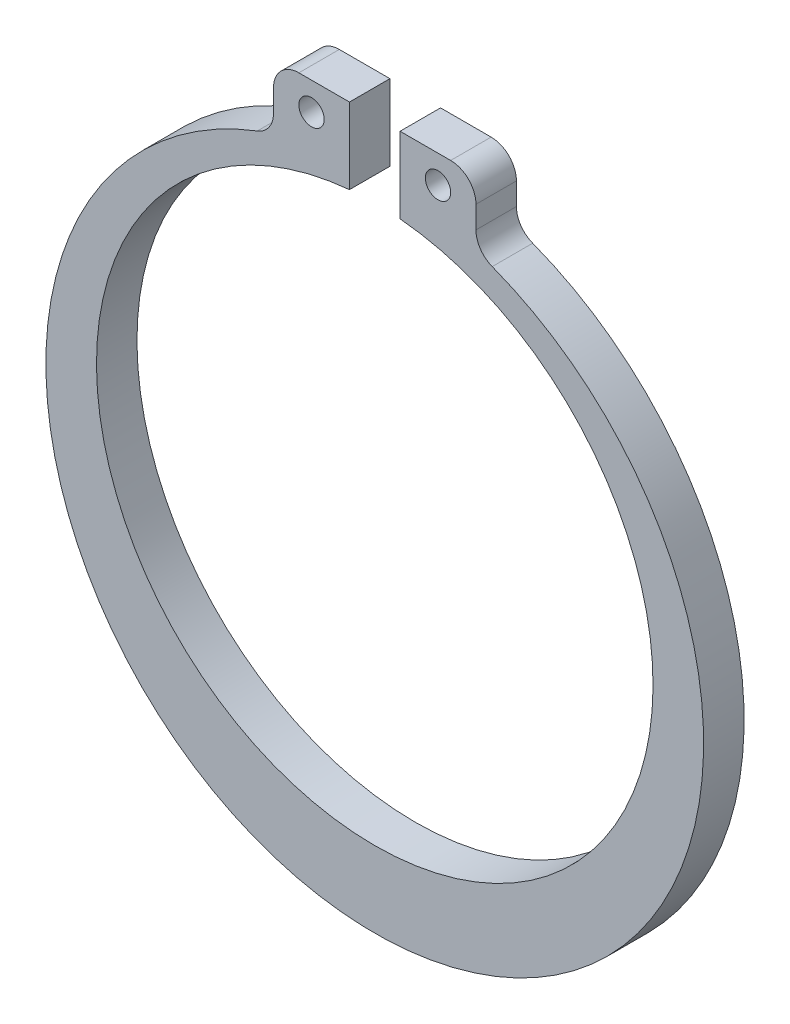
SolidWorks part; units mm, degrees
material "Сталь"
ref_plane "Спереди" through (0, 0, 0) normal (0, 0, 1) x (1, 0, 0)
ref_plane "Сверху" through (0, 0, 0) normal (0, 1, 0) x (1, 0, 0)
ref_plane "Справа" through (0, 0, 0) normal (1, 0, 0) x (0, 0, -1)
sketch "Эскиз1" plane through (0, 0, 0) normal (0, 0, 1) x (1, 0, 0)
  line L0 (0, -9.3116) -> (0, 9.3116) construction
  line L1 (0.5, 6.9772) -> (0.5, 5.4772)
  line L2 (0, -5.5) -> (0, -7)
  line L3 (0.5, 6.9772) -> (2, 6.9772)
  line L4 (2, 6.9772) -> (2, 5.6847)
  line L5 (1.25, 6.9772) -> (1.25, 5.8787) construction
  arc A0 (0, 5.5) -> (0, -5.5) centre (0, 0) cw
  arc A1 (0.5, 5.9807) -> (0, -7) centre (0, -0.5) cw
  circle A2 centre (1.25, 6.428) radius 0.25
  dimension "D1" = 5.5
  dimension "D4" = 6.5
  dimension "D7" = 0.5
  dimension "D2" = 0.5
  dimension "D3" = 0.5
  dimension "D5" = 1.5
  dimension "D6" = 1.5
extrude "Бобышка-Вытянуть1" add sketch "Эскиз1" along normal mid plane 0.8 contours L1 A1 L4 L3 A2 | A1 L1 A0 L2
fillet "Скругление1" radius 0.5 2 edges at (2, 5.6847, 0) (2, 6.9772, 0)
mirror "Зеркальное отражение1" about plane through (0, 0, 0.4) normal (1, 0, 0) of "Скругление1", "Бобышка-Вытянуть1"
